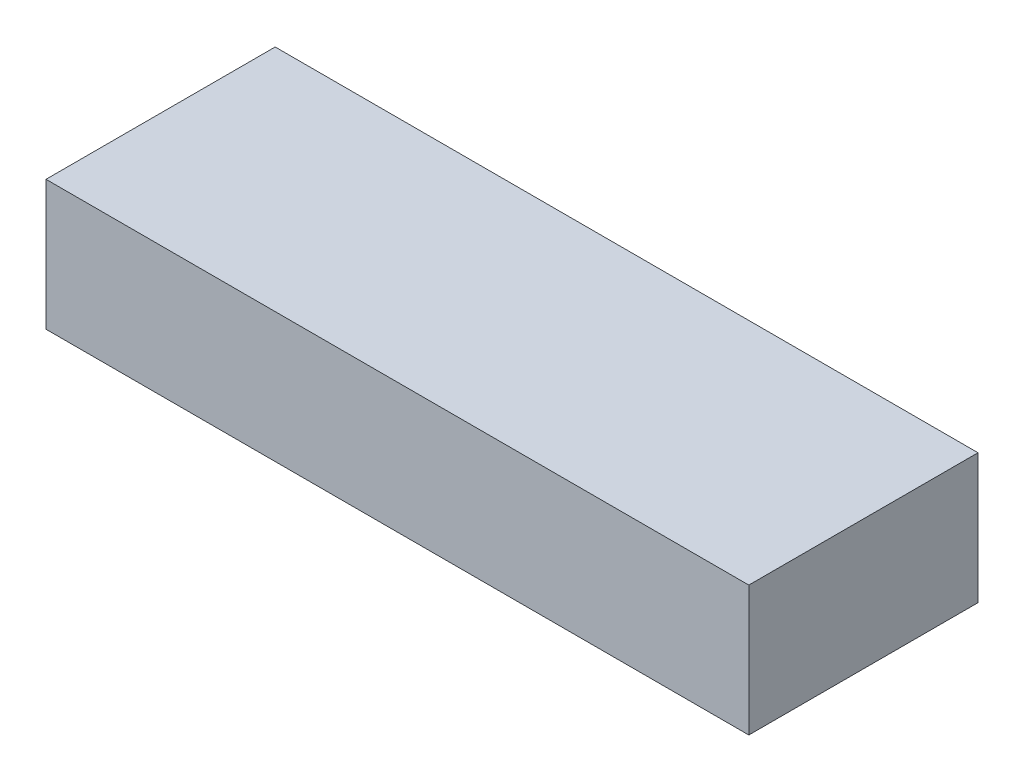
SolidWorks part; units mm, degrees
ref_plane "Plano frontal" through (0, 0, 0) normal (0, 0, 1) x (1, 0, 0)
ref_plane "Plano superior" through (0, 0, 0) normal (0, 1, 0) x (1, 0, 0)
ref_plane "Plano direito" through (0, 0, 0) normal (1, 0, 0) x (0, 0, -1)
sketch "Esboço1" plane through (0, 0, 0) normal (0, 1, 0) x (1, 0, 0)
  line L1 (-23, 7.5) -> (23, 7.5)
  line L2 (-23, 7.5) -> (-23, -7.5)
  line L3 (-23, -7.5) -> (23, -7.5)
  line L4 (23, 7.5) -> (23, -7.5)
  line L5 (-23, 7.5) -> (23, -7.5) construction
  line L6 (-23, -7.5) -> (23, 7.5) construction
  point P0 (0, 0)
  dimension "D1" = 46
  dimension "D2" = 15
extrude "Ressalto-extrusão1" add sketch "Esboço1" along normal blind 8.5
sketch "Esboço2" plane through (0, 8.5, 0) normal (0, 1, 0) x (1, 0, 0)
  line L0 (0, 0) -> (23, 0) construction
  line L1 (23, -7.5) -> (23, 7.5) construction
  line L2 (-23, 0) -> (0, 0) construction
  line L3 (-23, 7.5) -> (-23, -7.5) construction
  circle A0 centre (-11.5, 0) radius 2.75
  circle A1 centre (11.5, 0) radius 2.75
  dimension "D1" = 5.5
  dimension "D2" = 5.5
